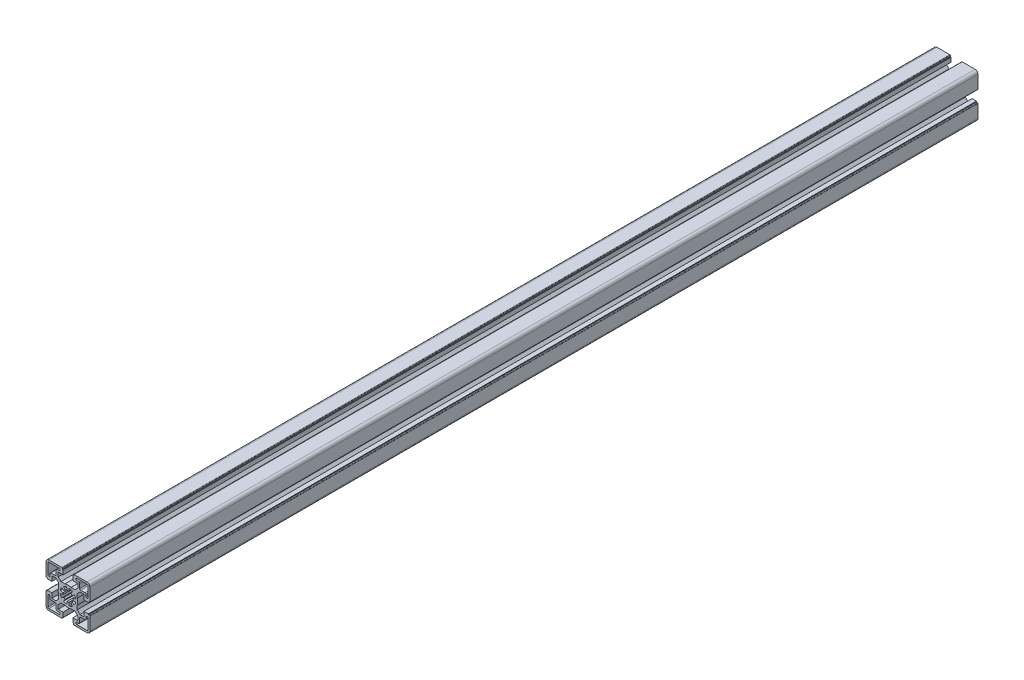
SolidWorks part; units mm, degrees
material "7079 Alloy"
ref_plane "Front Plane" through (0, 0, 0) normal (0, 0, 1) x (1, 0, 0)
ref_plane "Top Plane" through (0, 0, 0) normal (0, 1, 0) x (1, 0, 0)
ref_plane "Right Plane" through (0, 0, 0) normal (1, 0, 0) x (0, 0, -1)
sketch "Sketch1" plane through (0, 0, 0) normal (0, 0, 1) x (1, 0, 0)
  line L0 (0, 34.901) -> (0, -38.8683) construction
  line L1 (-27.7848, 0) -> (42.6814, 0) construction
  line L88 (0.8682, 4.924) -> (1.3892, 7.8784)
  line L89 (-0.8682, 4.924) -> (-1.3892, 7.8785)
  line L90 (-4.5886, 6.5532) -> (-2.8679, 4.0957)
  line L91 (-4.0957, 2.8679) -> (-6.5532, 4.5886)
  line L92 (-7.8784, 1.3892) -> (-4.924, 0.8682)
  line L93 (-7.8785, -1.3892) -> (-4.924, -0.8682)
  line L94 (-6.5532, -4.5886) -> (-4.0957, -2.8679)
  line L95 (-4.5886, -6.5532) -> (-2.8679, -4.0957)
  line L96 (-1.3892, -7.8784) -> (-0.8682, -4.924)
  line L97 (0.8682, -4.924) -> (1.3892, -7.8784)
  line L98 (4.5886, -6.5532) -> (2.8679, -4.0957)
  line L99 (4.0957, -2.8679) -> (6.5532, -4.5886)
  line L100 (7.8784, -1.3892) -> (4.924, -0.8682)
  line L101 (4.924, 0.8682) -> (7.8784, 1.3892)
  line L102 (4.0957, 2.8679) -> (6.5532, 4.5886)
  line L103 (2.8679, 4.0957) -> (4.5886, 6.5532)
  line L104 (-5, -16.4999) -> (-5, -20.9999)
  line L105 (-5, -20.9999) -> (-5.8, -20.9999)
  line L106 (-5.8, -20.9999) -> (-5.8, -22)
  line L107 (-6.3, -22.5) -> (-19.5, -22.5)
  line L108 (-22.5, -19.5) -> (-22.5, -6.2999)
  line L109 (-22, -5.7999) -> (-21, -5.7999)
  line L110 (-21, -5.7999) -> (-21, -4.9999)
  line L111 (-21, -4.9999) -> (-16.5, -4.9999)
  line L112 (-16.5, -4.9999) -> (-16.5, -10.0499)
  line L113 (-16.5, -10.0499) -> (-12.3429, -10.0499)
  line L114 (-12.3429, -10.0499) -> (-9.5, -7.207)
  line L115 (-9.5, -7.207) -> (-9.5, -3.1226)
  line L116 (-9.5, 3.1227) -> (-9.5, 7.207)
  line L117 (-9.5, 7.207) -> (-12.3429, 10.0499)
  line L118 (-12.3429, 10.0499) -> (-16.5, 10.0499)
  line L119 (-16.5, 10.0499) -> (-16.5, 4.9999)
  line L120 (-16.5, 4.9999) -> (-21, 4.9999)
  line L121 (-21, 4.9999) -> (-21, 5.7999)
  line L122 (-21, 5.7999) -> (-22, 5.7999)
  line L123 (-22.5, 6.2999) -> (-22.5, 19.5)
  line L124 (-19.5, 22.5) -> (-6.3, 22.5)
  line L125 (-5.7999, 21.9999) -> (-5.7999, 20.9999)
  line L126 (-5.7999, 20.9999) -> (-5, 20.9999)
  line L127 (-5, 20.9999) -> (-5, 16.5)
  line L128 (-5, 16.5) -> (-10.0501, 16.5)
  line L129 (-10.0501, 16.5) -> (-10.0501, 12.3428)
  line L130 (-10.0501, 12.3428) -> (-7.2072, 9.4999)
  line L131 (-7.2072, 9.4999) -> (-3.1228, 9.4999)
  line L132 (3.1226, 9.4999) -> (7.207, 9.4999)
  line L133 (7.207, 9.4999) -> (10.0499, 12.3428)
  line L134 (10.0499, 12.3428) -> (10.0499, 16.5)
  line L135 (10.0499, 16.5) -> (5, 16.5)
  line L136 (5, 16.5) -> (5, 21)
  line L137 (5, 21) -> (5.7999, 21)
  line L138 (5.7999, 21) -> (5.7999, 21.9999)
  line L139 (6.3, 22.5) -> (19.5001, 22.5)
  line L140 (22.5001, 6.2999) -> (22.5001, 19.5)
  line L141 (22.0001, 5.7999) -> (21, 5.7999)
  line L142 (21, 5.7999) -> (21, 4.9999)
  line L143 (21, 4.9999) -> (16.5, 4.9999)
  line L144 (16.5, 4.9999) -> (16.5, 10.0499)
  line L145 (16.5, 10.0499) -> (12.3429, 10.0499)
  line L146 (12.3429, 10.0499) -> (9.4999, 7.207)
  line L147 (9.4999, 7.207) -> (9.4999, 3.1227)
  line L148 (9.4999, -3.1226) -> (9.4999, -7.207)
  line L149 (9.4999, -7.207) -> (12.3429, -10.0499)
  line L150 (12.3429, -10.0499) -> (16.5, -10.0499)
  line L151 (16.5, -10.0499) -> (16.5, -4.9999)
  line L152 (16.5, -4.9999) -> (21, -4.9999)
  line L153 (21, -4.9999) -> (21, -5.7999)
  line L154 (21, -5.7999) -> (22.0001, -5.7999)
  line L155 (22.5001, -6.2999) -> (22.5001, -19.5)
  line L156 (6.3, -22.5) -> (19.5001, -22.5)
  line L157 (5.8, -22) -> (5.8, -20.9999)
  line L158 (5.8, -20.9999) -> (5, -20.9999)
  line L159 (5, -20.9999) -> (5, -16.4999)
  line L160 (5, -16.4999) -> (10.0499, -16.4999)
  line L161 (10.0499, -16.4999) -> (10.0499, -12.3428)
  line L162 (10.0499, -12.3428) -> (7.2069, -9.4998)
  line L163 (7.2069, -9.4998) -> (3.1226, -9.4998)
  line L164 (-3.1228, -9.4998) -> (-7.2071, -9.4998)
  line L165 (-7.2071, -9.4998) -> (-10.0501, -12.3428)
  line L166 (-10.0501, -12.3428) -> (-10.0501, -16.4999)
  line L167 (-10.0501, -16.4999) -> (-5, -16.4999)
  line L168 (-17.5001, -12) -> (-13.0001, -12)
  line L169 (-12.0001, -17.4999) -> (-12.0001, -13)
  line L170 (-11.0001, -18.4999) -> (-9.0001, -18.4999)
  line L171 (-19.5001, -20.5) -> (-9.0001, -20.5)
  line L172 (-20.5001, -19.5) -> (-20.5001, -8.9999)
  line L173 (-18.5001, -11) -> (-18.5001, -8.9999)
  line L174 (13, -12) -> (17.5, -12)
  line L175 (12, -17.4999) -> (12, -13)
  line L176 (9, -18.4999) -> (11, -18.4999)
  line L177 (9, -20.5) -> (19.5, -20.5)
  line L178 (20.5, -19.5) -> (20.5, -9.0001)
  line L179 (18.5, -11) -> (18.5, -9.0001)
  line L180 (-17.5001, 12) -> (-13.0001, 12)
  line L181 (-12.0001, 13) -> (-12.0001, 17.4999)
  line L182 (-11.0001, 18.4999) -> (-9.0001, 18.4999)
  line L183 (-19.5001, 20.5) -> (-9.0001, 20.5)
  line L184 (-20.5001, 8.9999) -> (-20.5001, 19.5)
  line L185 (-18.5001, 8.9999) -> (-18.5001, 11)
  line L186 (13, 12) -> (17.5, 12)
  line L187 (12, 13) -> (12, 17.4999)
  line L188 (9, 18.4999) -> (11, 18.4999)
  line L189 (9, 20.5) -> (19.5, 20.5)
  line L190 (20.5, 9.0001) -> (20.5, 19.5)
  line L191 (18.5, 9.0001) -> (18.5, 11)
  arc A56 (0.8682, 4.924) -> (-0.8682, 4.924) centre (0, 0) ccw
  arc A57 (-1.3892, 7.8785) -> (-4.5886, 6.5532) centre (0, 0) ccw
  arc A58 (-2.8679, 4.0957) -> (-4.0957, 2.8679) centre (0, 0) ccw
  arc A59 (-6.5532, 4.5886) -> (-7.8784, 1.3892) centre (0, 0) ccw
  arc A60 (-4.924, 0.8682) -> (-4.924, -0.8682) centre (0, 0) ccw
  arc A61 (-7.8785, -1.3892) -> (-6.5532, -4.5886) centre (0, 0) ccw
  arc A62 (-4.0957, -2.8679) -> (-2.8679, -4.0957) centre (0, 0) ccw
  arc A63 (-4.5886, -6.5532) -> (-1.3892, -7.8784) centre (0, 0) ccw
  arc A64 (-0.8682, -4.924) -> (0.8682, -4.924) centre (0, 0) ccw
  arc A65 (1.3892, -7.8784) -> (4.5886, -6.5532) centre (0, 0) ccw
  arc A66 (2.8679, -4.0957) -> (4.0957, -2.8679) centre (0, 0) ccw
  arc A67 (6.5532, -4.5886) -> (7.8784, -1.3892) centre (0, 0) ccw
  arc A68 (4.924, -0.8682) -> (4.924, 0.8682) centre (0, 0) ccw
  arc A69 (7.8784, 1.3892) -> (6.5532, 4.5886) centre (0, 0) ccw
  arc A70 (4.0957, 2.8679) -> (2.8679, 4.0957) centre (0, 0) ccw
  arc A71 (4.5886, 6.5532) -> (1.3892, 7.8784) centre (0, 0) ccw
  arc A72 (-6.3, -22.5) -> (-5.8, -22) centre (-6.3, -22) ccw
  arc A73 (-22.5, -19.5) -> (-19.5, -22.5) centre (-19.5, -19.5) ccw
  arc A74 (-22, -5.7999) -> (-22.5, -6.2999) centre (-22, -6.2999) ccw
  arc A75 (-9.5, 3.1227) -> (-9.5, -3.1226) centre (0, 0.0001) ccw
  arc A76 (-22.5, 6.2999) -> (-22, 5.7999) centre (-22, 6.2999) ccw
  arc A77 (-19.5, 22.5) -> (-22.5, 19.5) centre (-19.5, 19.5) ccw
  arc A78 (-5.7999, 21.9999) -> (-6.3, 22.5) centre (-6.3, 21.9999) ccw
  arc A79 (3.1226, 9.4999) -> (-3.1228, 9.4999) centre (-0.0001, -0.0001) ccw
  arc A80 (6.3, 22.5) -> (5.7999, 21.9999) centre (6.3, 21.9999) ccw
  arc A81 (22.5001, 19.5) -> (19.5001, 22.5) centre (19.5001, 19.5) ccw
  arc A82 (22.0001, 5.7999) -> (22.5001, 6.2999) centre (22.0001, 6.2999) ccw
  arc A83 (9.4999, -3.1226) -> (9.4999, 3.1227) centre (0, 0.0001) ccw
  arc A84 (22.5001, -6.2999) -> (22.0001, -5.7999) centre (22.0001, -6.2999) ccw
  arc A85 (19.5001, -22.5) -> (22.5001, -19.5) centre (19.5001, -19.5) ccw
  arc A86 (5.8, -22) -> (6.3, -22.5) centre (6.3, -22) ccw
  arc A87 (-3.1228, -9.4998) -> (3.1226, -9.4998) centre (-0.0001, 0.0001) ccw
  arc A88 (-18.5001, -11) -> (-17.5001, -12) centre (-17.5001, -11) ccw
  arc A89 (-12.0001, -13) -> (-13.0001, -12) centre (-13.0001, -13) ccw
  arc A90 (-12.0001, -17.4999) -> (-11.0001, -18.4999) centre (-11.0001, -17.4999) ccw
  arc A91 (-9.0001, -20.5) -> (-9.0001, -18.4999) centre (-9.0001, -19.5) ccw
  arc A92 (-20.5001, -19.5) -> (-19.5001, -20.5) centre (-19.5001, -19.5) ccw
  arc A93 (-18.5001, -8.9999) -> (-20.5001, -8.9999) centre (-19.5001, -8.9999) ccw
  arc A94 (17.5, -12) -> (18.5, -11) centre (17.5, -11) ccw
  arc A95 (13, -12) -> (12, -13) centre (13, -13) ccw
  arc A96 (11, -18.4999) -> (12, -17.4999) centre (11, -17.4999) ccw
  arc A97 (9, -18.4999) -> (9, -20.5) centre (9, -19.5) ccw
  arc A98 (19.5, -20.5) -> (20.5, -19.5) centre (19.5, -19.5) ccw
  arc A99 (20.5, -9.0001) -> (18.5, -9.0001) centre (19.5, -9.0001) ccw
  arc A100 (-17.5001, 12) -> (-18.5001, 11) centre (-17.5001, 11) ccw
  arc A101 (-13.0001, 12) -> (-12.0001, 13) centre (-13.0001, 13) ccw
  arc A102 (-11.0001, 18.4999) -> (-12.0001, 17.4999) centre (-11.0001, 17.4999) ccw
  arc A103 (-9.0001, 18.4999) -> (-9.0001, 20.5) centre (-9.0001, 19.5) ccw
  arc A104 (-19.5001, 20.5) -> (-20.5001, 19.5) centre (-19.5001, 19.5) ccw
  arc A105 (-20.5001, 8.9999) -> (-18.5001, 8.9999) centre (-19.5001, 8.9999) ccw
  arc A106 (18.5, 11) -> (17.5, 12) centre (17.5, 11) ccw
  arc A107 (12, 13) -> (13, 12) centre (13, 13) ccw
  arc A108 (12, 17.4999) -> (11, 18.4999) centre (11, 17.4999) ccw
  arc A109 (9, 20.5) -> (9, 18.4999) centre (9, 19.5) ccw
  arc A110 (20.5, 19.5) -> (19.5, 20.5) centre (19.5, 19.5) ccw
  arc A111 (18.5, 9.0001) -> (20.5, 9.0001) centre (19.5, 9.0001) ccw
  dimension "D5" = 10
  dimension "D1" = 45.0001
  dimension "D2" = 44.9999
  dimension "D3" = 12.5001
  dimension "D4" = 10
  dimension "D6" = 22.5001
extrude "Base-Extrude" add sketch "Sketch1" along normal blind 910
